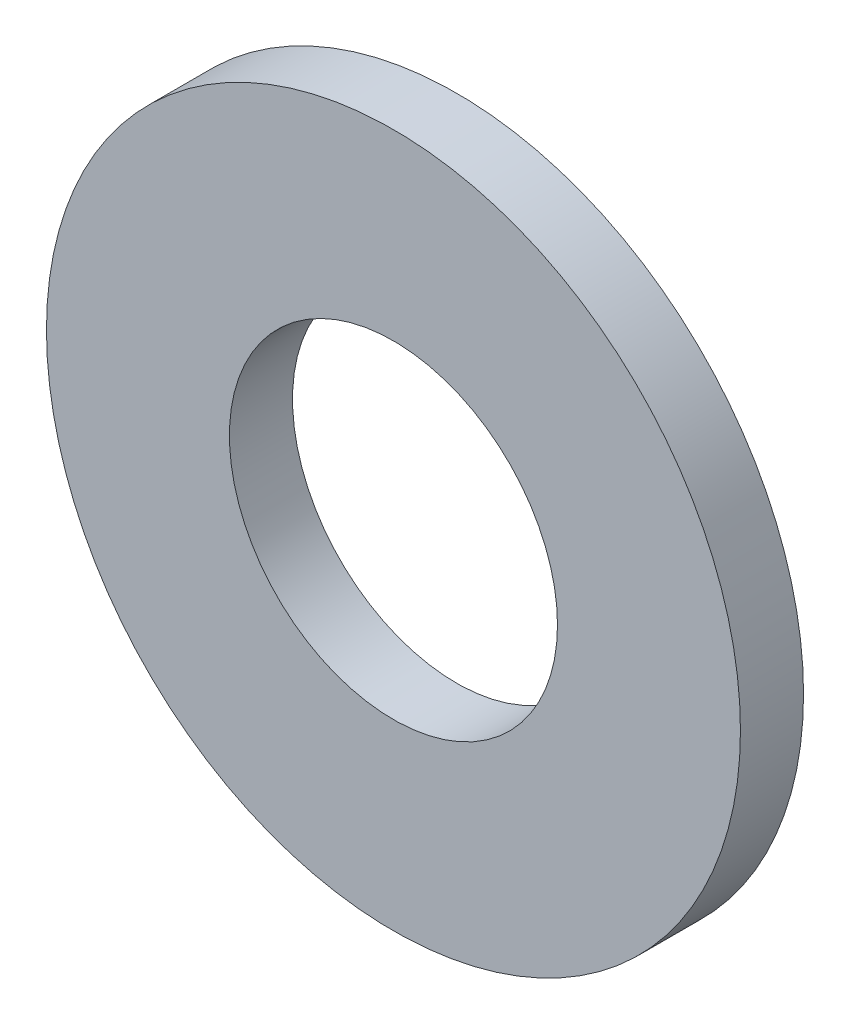
SolidWorks part; units mm, degrees
material "Plain Carbon Steel"
ref_plane "Front Plane" through (0, 0, 0) normal (0, 0, 1) x (1, 0, 0)
ref_plane "Top Plane" through (0, 0, 0) normal (0, 1, 0) x (1, 0, 0)
ref_plane "Right Plane" through (0, 0, 0) normal (1, 0, 0) x (0, 0, -1)
sketch "Sketch1" plane through (0, 0, 0) normal (0, 0, 1) x (1, 0, 0)
  circle A0 centre (0, 0) radius 5.5
  circle A1 centre (0, 0) radius 2.6
  dimension "D1" = 11
  dimension "D2" = 5.2
extrude "Boss-Extrude1" add sketch "Sketch1" along normal blind 1
